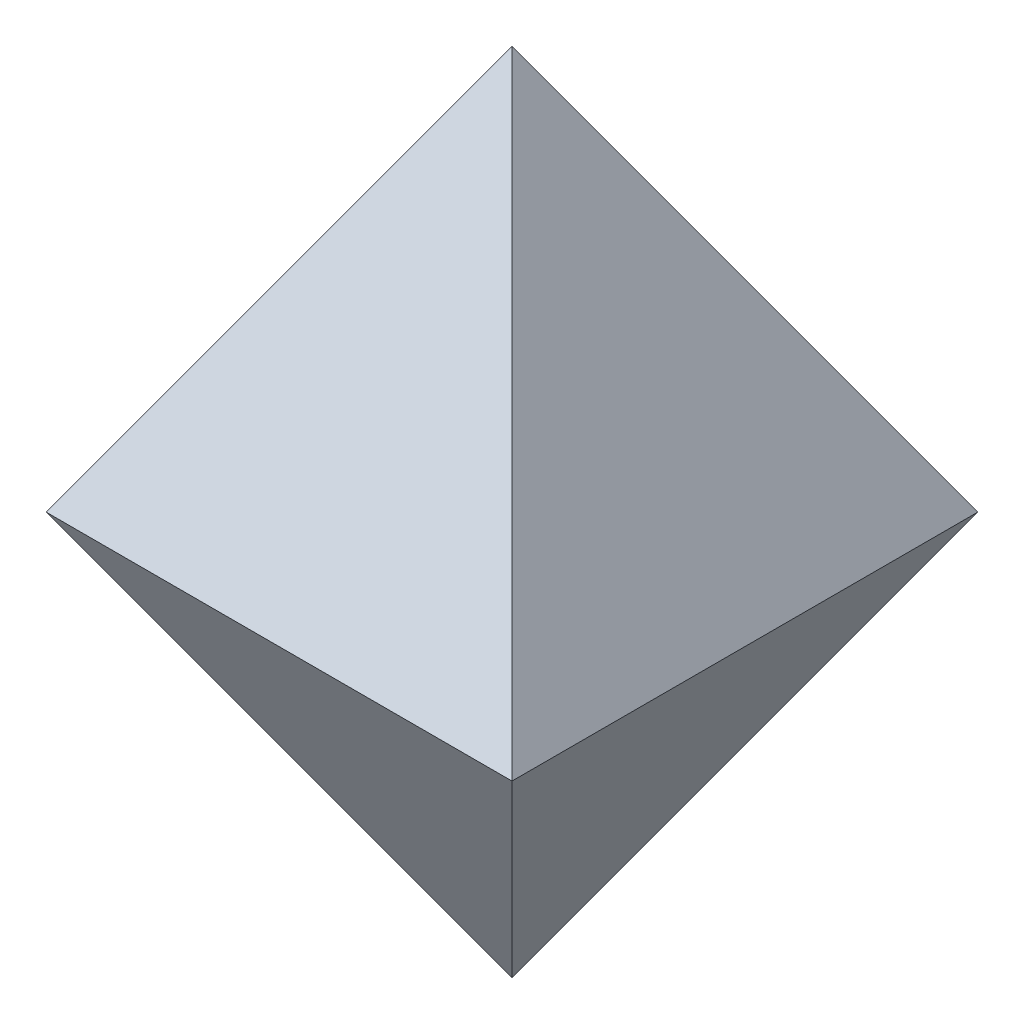
SolidWorks part; units mm, degrees
ref_plane "Front Plane" through (0, 0, 0) normal (0, 0, 1) x (1, 0, 0)
ref_plane "Top Plane" through (0, 0, 0) normal (0, 1, 0) x (1, 0, 0)
ref_plane "Right Plane" through (0, 0, 0) normal (1, 0, 0) x (0, 0, -1)
sketch "Sketch1" plane through (0, 0, 0) normal (0, 1, 0) x (1, 0, 0)
  line L1 (-5, -5) -> (5, -5)
  line L2 (-5, -5) -> (-5, 5)
  line L3 (-5, 5) -> (5, 5)
  line L4 (5, -5) -> (5, 5)
  line L5 (-5, -5) -> (5, 5) construction
  line L6 (-5, 5) -> (5, -5) construction
  point P0 (0, 0)
  dimension "D1" = 10
sketch "Sketch2" plane through (0, 0, 0) normal (0, 0, 1) x (1, 0, 0)
  line L0 (0, 0) -> (0, 8.6603)
  line L2 (0, 8.6603) -> (-5, 0)
  line L3 (-5, 0) -> (5, 0) construction
  line L5 (-5, 0) -> (0, 0)
  line L6 (-5, 0) -> (5, 0) construction
  line L7 (-5, 0) -> (5, 0) construction
  point P3 (0, 0)
  dimension "D1" = 60
extrude "Boss-Extrude1" add sketch "Sketch1" along normal up to vertex (8.6603 mm away) draft 30 up to point (0, 8.6603, 0)
mirror "Mirror1" about plane through (0, 0, 0) normal (0, -1, 0) of "Boss-Extrude1"
